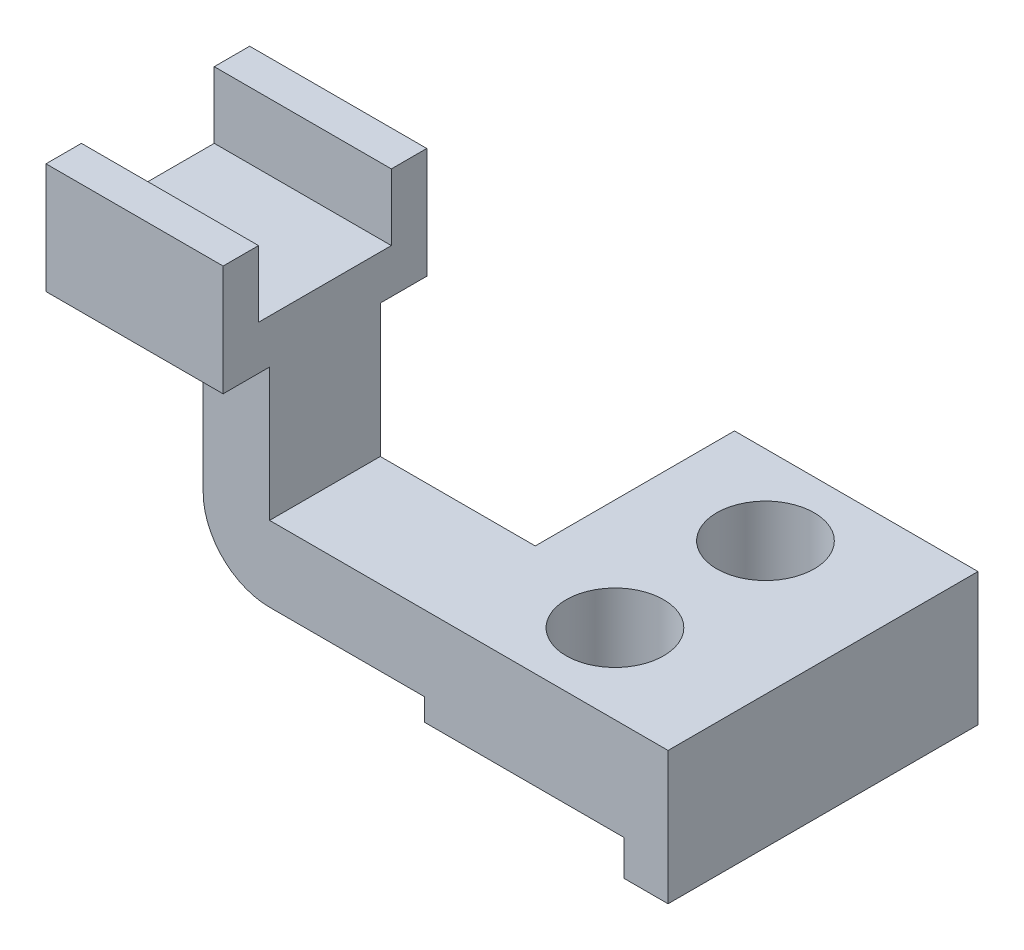
SolidWorks part; units mm, degrees
ref_plane "Front Plane" through (0, 0, 0) normal (0, 0, 1) x (1, 0, 0)
ref_plane "Top Plane" through (0, 0, 0) normal (0, 1, 0) x (1, 0, 0)
ref_plane "Right Plane" through (0, 0, 0) normal (1, 0, 0) x (0, 0, -1)
sketch "Sketch2" plane through (0, 0, 0) normal (0, 1, 0) x (1, 0, 0)
  line L0 (-63.9822, 1.2957) -> (-63.9822, -23.7043)
  line L1 (-63.9822, -23.7043) -> (26.0178, -23.7043)
  line L3 (26.0178, 46.2957) -> (-28.9822, 46.2957)
  line L4 (-28.9822, 46.2957) -> (-28.9822, 1.2957)
  line L5 (-63.9822, 1.2957) -> (-28.9822, 1.2957)
  line L6 (26.0178, 46.2957) -> (26.0178, -23.7043)
  line L7 (26.0178, 71.6496) -> (26.0178, -62.1309) construction
  circle A0 centre (-3.9822, -5.7043) radius 11
  circle A1 centre (-3.9822, 28.2957) radius 11
extrude "Boss-Extrude1" add sketch "Sketch2" along normal blind 30
sketch "Sketch3" plane through (0, 0, 23.7043) normal (0, 0, 1) x (1, 0, 0)
  line L0 (26.0178, 30) -> (26.0178, 0)
  line L1 (55, 0) -> (-55, 0) construction
  line L2 (26.0178, 30) -> (26.0178, 0) construction
  line L4 (16.0178, 0) -> (16.0178, 8)
  line L5 (16.0178, 8) -> (-28.9822, 8)
  line L6 (-28.9822, 8) -> (-28.9822, 13)
  line L7 (-28.9822, 13) -> (-63.9822, 13)
  line L8 (-63.9822, 30) -> (-63.9822, 0) construction
  line L9 (-63.9822, 13) -> (-63.9822, 0)
  line L10 (-63.9822, 0) -> (16.0178, 0)
  line M1 (-63.9822, 0) -> (26.0178, 0)
  line M4 (-63.9822, 30) -> (-63.9822, 0)
extrude "Cut-Extrude1" cut sketch "Sketch3" against normal blind 70 contours L6 L7 L4 L5 M4 M1
sketch3d "3DSketch1"
  line L0 (-63.9822, 13, -1.2957) -> (-63.9822, 13, 23.7043)
  line L1 (-63.9822, 13, 23.7043) -> (-63.9822, 60, 23.7043)
  line L2 (-63.9822, 60, 23.7043) -> (-63.9822, 60, 34.2043)
  line L3 (-63.9822, 60, 34.2043) -> (-63.9822, 85, 34.2043)
  line L4 (-63.9822, 85, 34.2043) -> (-63.9822, 85, 26.2043)
  line L5 (-63.9822, 85, 26.2043) -> (-63.9822, 70, 26.2043)
  line L6 (-63.9822, 70, 26.2043) -> (-63.9822, 70, -3.7957)
  line L7 (-63.9822, 70, -3.7957) -> (-63.9822, 85, -3.7957)
  line L8 (-63.9822, 85, -3.7957) -> (-63.9822, 85, -11.7957)
  line L9 (-63.9822, 85, -11.7957) -> (-63.9822, 60, -11.7957)
  line L10 (-63.9822, 60, -11.7957) -> (-63.9822, 60, -1.2957)
  line L11 (-63.9822, 60, -1.2957) -> (-63.9822, 13, -1.2957)
extrude "Boss-Extrude3" add sketch "3DSketch1" along direction (1, 0, 0) on the side of the normal blind 40 contours L0 L1 L2 L3 L4 L5 L6 L7 L8 L9 L10 L11
sketch "Sketch4" plane through (0, 0, 23.7043) normal (0, 0, 1) x (1, 0, 0)
  line L0 (-103.9822, 13) -> (-78.9822, 13)
  line L1 (-28.9822, 13) -> (-103.9822, 13) construction
  line L2 (-78.9822, 13) -> (-78.9822, 60)
  line L3 (-63.9822, 60) -> (-103.9822, 60) construction
  line L4 (-78.9822, 60) -> (-103.9822, 60)
  line L5 (-103.9822, 60) -> (-103.9822, 13)
extrude "Cut-Extrude2" cut sketch "Sketch4" against normal blind 46
fillet "Fillet1" radius 15 1 edges at (-78.9822, 13, 11.2043)
